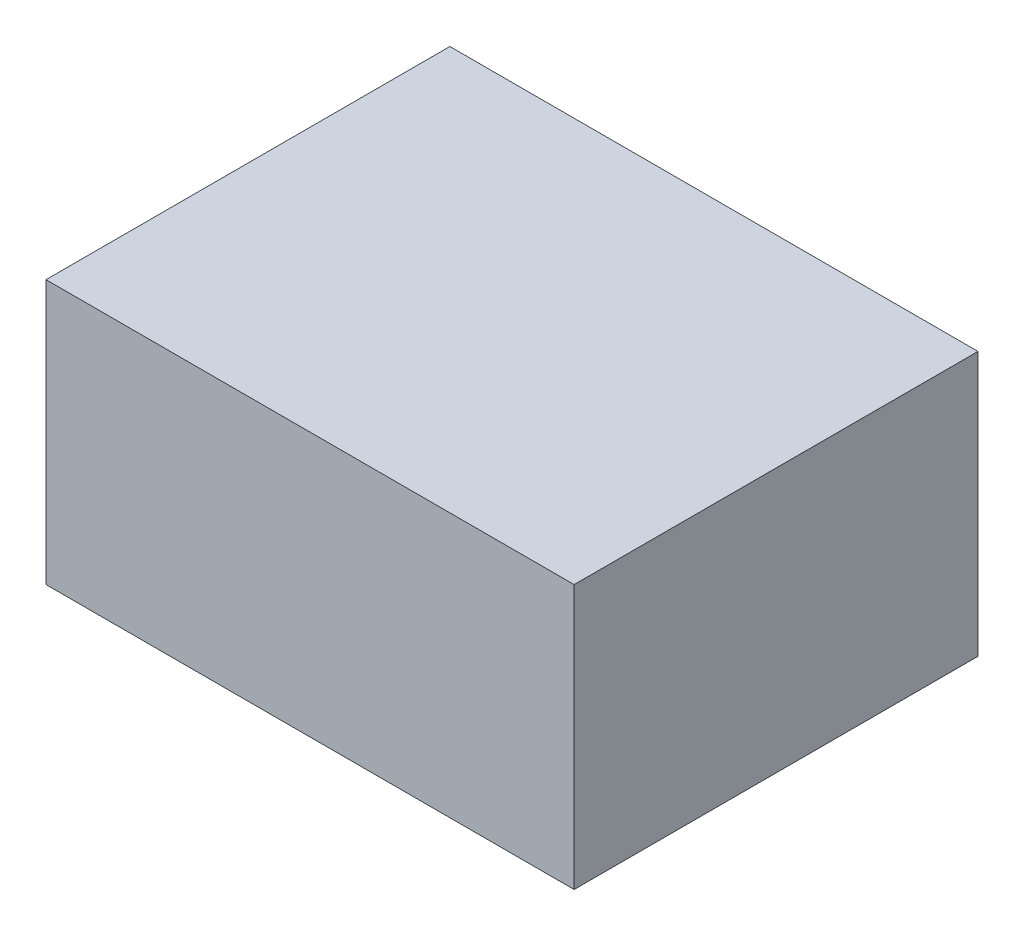
SolidWorks part; units mm, degrees
material "1060-H18"
ref_plane "Front Plane" through (0, 0, 0) normal (0, 0, 1) x (1, 0, 0)
ref_plane "Top Plane" through (0, 0, 0) normal (0, 1, 0) x (1, 0, 0)
ref_plane "Right Plane" through (0, 0, 0) normal (1, 0, 0) x (0, 0, -1)
sketch "Sketch1" plane through (0, 0, 0) normal (0, 1, 0) x (1, 0, 0)
  line L1 (-0.17, -0.13) -> (0.17, -0.13)
  line L2 (-0.17, -0.13) -> (-0.17, 0.13)
  line L3 (-0.17, 0.13) -> (0.17, 0.13)
  line L4 (0.17, -0.13) -> (0.17, 0.13)
  line L5 (-0.17, -0.13) -> (0.17, 0.13) construction
  line L6 (-0.17, 0.13) -> (0.17, -0.13) construction
  point P0 (0, 0)
  dimension "D1" = 0.34
  dimension "D2" = 0.26
extrude "Boss-Extrude1" add sketch "Sketch1" along normal blind 0.17
